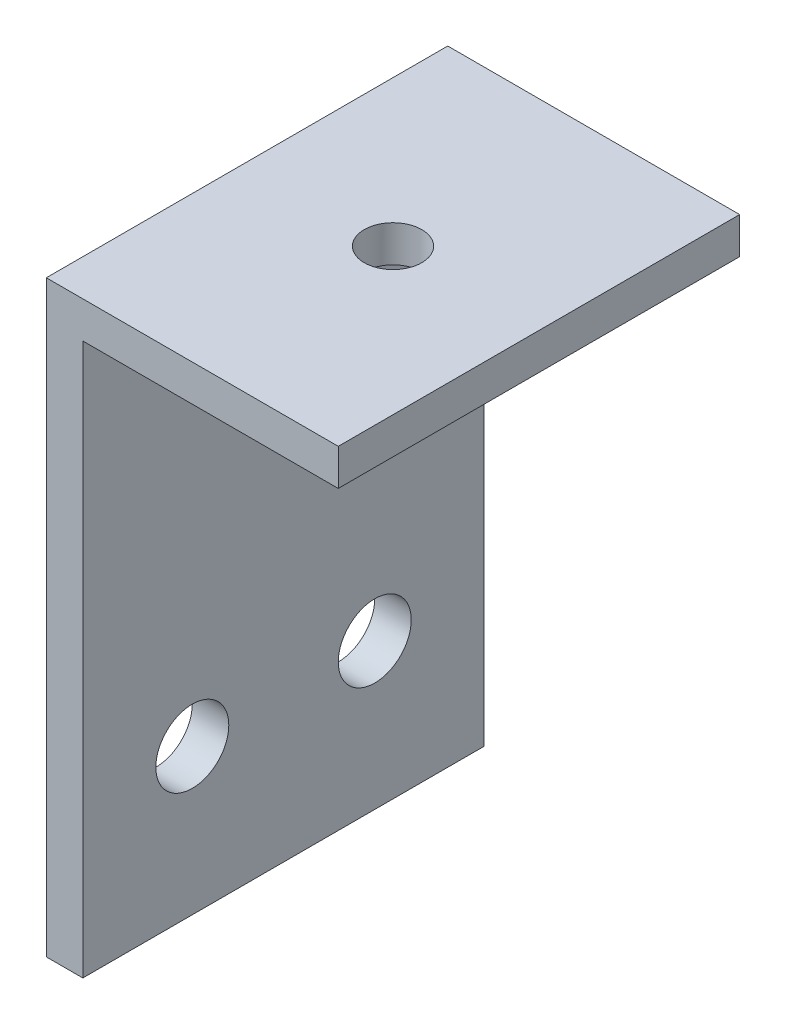
SolidWorks part; units mm, degrees
ref_plane "Front Plane" through (0, 0, 0) normal (0, 0, 1) x (1, 0, 0)
ref_plane "Top Plane" through (0, 0, 0) normal (0, 1, 0) x (1, 0, 0)
ref_plane "Right Plane" through (0, 0, 0) normal (1, 0, 0) x (0, 0, -1)
sketch "Sketch1" plane through (0, 0, 0) normal (0, 0, 1) x (1, 0, 0)
  line L1 (0, 0) -> (3.175, 0)
  line L2 (0, 0) -> (0, 51.175)
  line L3 (0, 51.175) -> (25.4, 51.175)
  line L4 (25.4, 48) -> (25.4, 51.175)
  line L7 (25.4, 48) -> (3.175, 48)
  line L8 (3.175, 0) -> (3.175, 48)
  dimension "D1" = 51.175
  dimension "D2" = 25.4
  dimension "D3" = 3.175
  dimension "D4" = 3.175
extrude "Boss-Extrude1" add sketch "Sketch1" along normal blind 34.925
sketch "Sketch2" plane through (3.175, 0, 0) normal (1, 0, 0) x (0, 0, -1)
  line L0 (-34.925, 0) -> (0, 0) construction
  line L1 (-34.925, 0) -> (-34.925, 48) construction
  line L2 (0, 0) -> (0, 48) construction
  circle A0 centre (-25.4, 12.7) radius 3.175
  circle A1 centre (-9.525, 12.7) radius 3.175
  dimension "D1" = 6.35
  dimension "D2" = 12.7
  dimension "D3" = 9.525
  dimension "D4" = 9.525
extrude "Cut-Extrude1" cut sketch "Sketch2" against normal through all
sketch "Sketch3" plane through (0, 51.175, 0) normal (0, 1, 0) x (1, 0, 0)
  line L0 (25.4, 0) -> (0, 0) construction
  line L1 (0, -34.925) -> (0, 0) construction
  circle A0 centre (12.7, -17.4625) radius 2.5
  dimension "D1" = 5
  dimension "D2" = 12.7
  dimension "D3" = 17.4625
extrude "Cut-Extrude2" cut sketch "Sketch3" against normal through all
